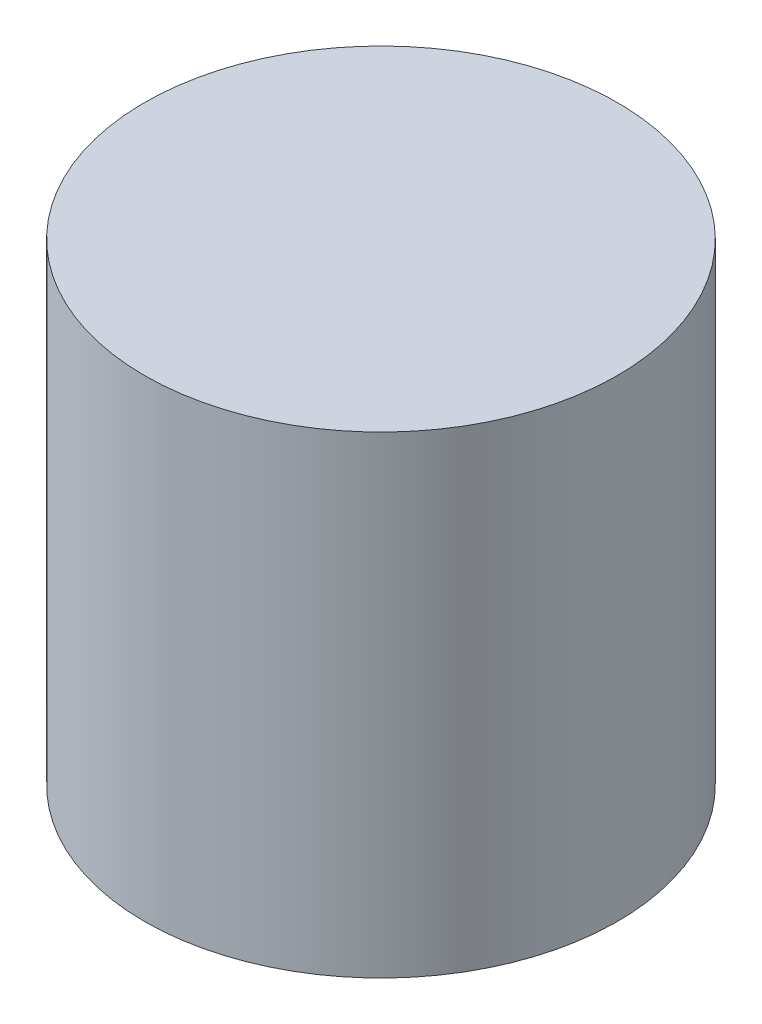
SolidWorks part; units mm, degrees
ref_plane "前视基准面" through (0, 0, 0) normal (0, 0, 1) x (1, 0, 0)
ref_plane "上视基准面" through (0, 0, 0) normal (0, 1, 0) x (1, 0, 0)
ref_plane "右视基准面" through (0, 0, 0) normal (1, 0, 0) x (0, 0, -1)
sketch "草图1" plane through (0, 0, 0) normal (0, 1, 0) x (1, 0, 0)
  circle A0 centre (0, 0) radius 20
  dimension "D1" = 40
extrude "凸台-拉伸1" add sketch "草图1" along normal blind 40 contours A0
